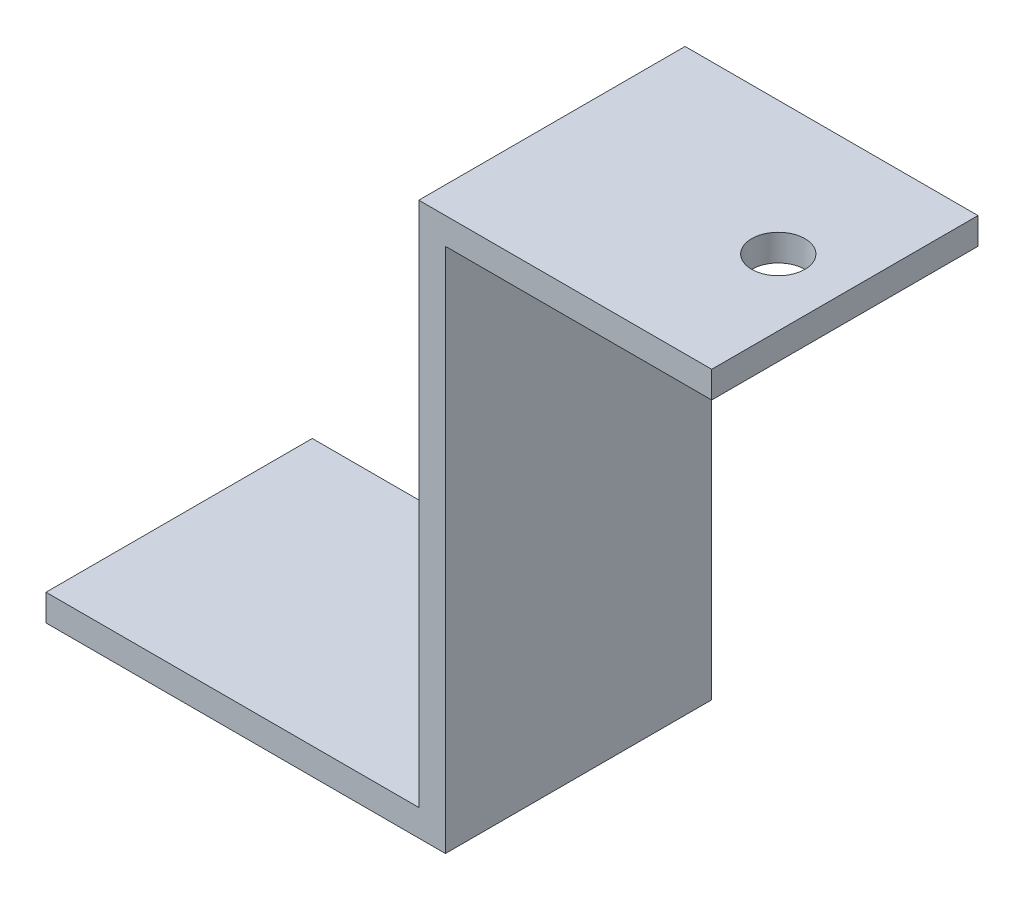
SolidWorks part; units mm, degrees
ref_plane "前视基准面" through (0, 0, 0) normal (0, 0, 1) x (1, 0, 0)
ref_plane "上视基准面" through (0, 0, 0) normal (0, 1, 0) x (1, 0, 0)
ref_plane "右视基准面" through (0, 0, 0) normal (1, 0, 0) x (0, 0, -1)
sketch "草图1" plane through (0, 0, 0) normal (0, 0, 1) x (1, 0, 0)
  line L0 (-17.1756, 38.8603) -> (-7.1756, 38.8603)
  line L1 (-7.1756, 38.8603) -> (2.8244, 38.8603)
  line L2 (2.8244, 38.8603) -> (2.8244, 36.8603)
  line L3 (2.8244, 36.8603) -> (-17.1756, 36.8603)
  line L4 (-17.1756, 36.8603) -> (-17.1756, -0.6397)
  line L5 (-17.1756, -0.6397) -> (-17.1756, -2.6397)
  line L6 (-17.1756, -2.6397) -> (-47.1756, -2.6397)
  line L7 (-47.1756, -2.6397) -> (-47.1756, -0.6397)
  line L8 (-47.1756, -0.6397) -> (-19.1756, -0.6397)
  line L9 (-19.1756, -0.6397) -> (-19.1756, 38.8603)
  line L10 (-19.1756, 38.8603) -> (-17.1756, 38.8603)
  dimension "D7" = 2
  dimension "D1" = 10
  dimension "D2" = 10
  dimension "D3" = 2
  dimension "D4" = 37.5
  dimension "D5" = 2
  dimension "D6" = 30
  dimension "D8" = 28
extrude "凸台-拉伸1" add sketch "草图1" along normal blind 20
sketch "草图2" plane through (0, 38.8603, 0) normal (0, 1, 0) x (1, 0, 0)
  line L0 (2.8244, -10) -> (-2.1756, -10) construction
  line L1 (2.8244, -20) -> (2.8244, 0) construction
  circle A0 centre (-2.1756, -10) radius 2
  dimension "D2" = 4
  dimension "D1" = 5
extrude "切除-拉伸1" cut sketch "草图2" against normal blind 20
